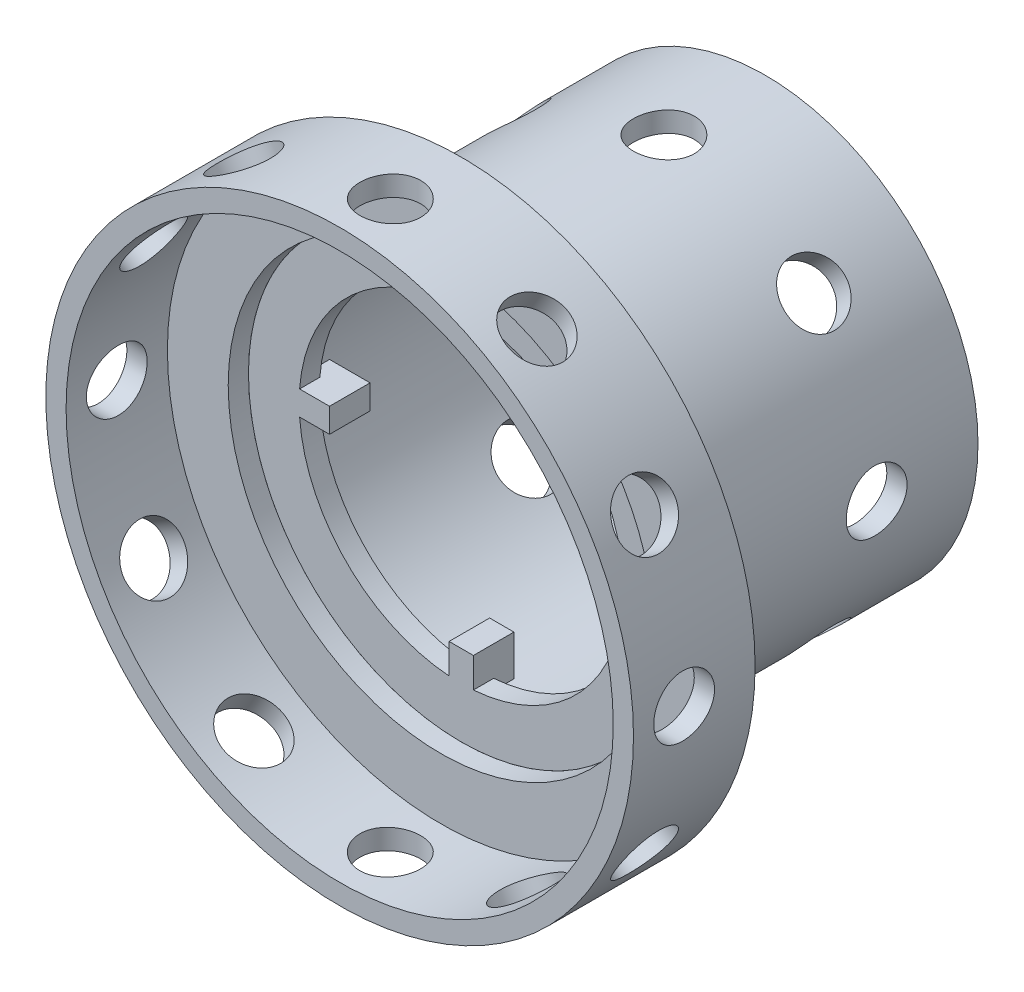
SolidWorks part; units mm, degrees
ref_plane "正面" through (0, 0, 0) normal (0, 0, 1) x (1, 0, 0)
ref_plane "平面" through (0, 0, 0) normal (0, 1, 0) x (1, 0, 0)
ref_plane "右側面" through (0, 0, 0) normal (1, 0, 0) x (0, 0, -1)
sketch "ｽｹｯﾁ1" plane through (0, 0, 0) normal (0, 0, 1) x (1, 0, 0)
  circle A0 centre (0, 0) radius 10.5
  circle A1 centre (0, 0) radius 9.5
  dimension "D1" = 21
  dimension "D2" = 19
extrude "ﾎﾞｽ - 押し出し1" add sketch "ｽｹｯﾁ1" along normal blind 15 from offset 10
sketch "ｽｹｯﾁ2" plane through (0, 0, 0) normal (0, 0, 1) x (1, 0, 0)
  circle A0 centre (0, 0) radius 10.5
  dimension "D1" = 21
extrude "ﾎﾞｽ - 押し出し2" [suppressed] add sketch "ｽｹｯﾁ2" along normal blind 1
sketch "ｽｹｯﾁ3" plane through (0, 0, 0) normal (0, 0, 1) x (1, 0, 0)
  circle A0 centre (4.4131, 3.5977) radius 0.493
extrude "ｶｯﾄ - 押し出し1" [suppressed] cut sketch "ｽｹｯﾁ3" along normal blind 1
sketch "ｽｹｯﾁ4" plane through (0, 0, 0) normal (0, 0, 1) x (1, 0, 0)
  circle A0 centre (0, 0) radius 7.5
  dimension "D1" = 15
sketch "ｽｹｯﾁ5" plane through (0, 0, 25) normal (0, 0, 1) x (1, 0, 0)
  line L1 (8.5, -0.6) -> (6.5, -0.6)
  line L2 (8.5, -0.6) -> (8.5, 0.6)
  line L3 (8.5, 0.6) -> (6.5, 0.6)
  line L4 (6.5, -0.6) -> (6.5, 0.6)
  line L5 (8.5, -0.6) -> (6.5, 0.6) construction
  line L6 (8.5, 0.6) -> (6.5, -0.6) construction
  circle A0 centre (0, 0) radius 7.5 construction
  point P0 (7.5, 0)
  point P8 (10.5, 0)
  dimension "D1" = 1.2
  dimension "D2" = 2
sketch "ｽｹｯﾁ6" plane through (0, 0, 0) normal (0, 0, 1) x (1, 0, 0)
  circle A0 centre (0, 0) radius 10
  circle A1 centre (0, 0) radius 8
  dimension "D1" = 20
  dimension "D2" = 16
extrude "ﾎﾞｽ - 押し出し3" add sketch "ｽｹｯﾁ6" against normal blind 1 from offset 25
extrude "ﾎﾞｽ - 押し出し4" add sketch "ｽｹｯﾁ5" against normal blind 2
pattern_circular "円形ﾊﾟﾀｰﾝ1" count 4 over 360 about axis through (0, 0, 0) along (0, 0, 1) of "ﾎﾞｽ - 押し出し4"
sketch "ｽｹｯﾁ7" plane through (0, 0, 0) normal (1, 0, 0) x (0, 0, -1)
  line L0 (-10, -10.5) -> (-10, 10.5) construction
  circle A0 centre (-15, 0) radius 1.5
  dimension "D1" = 3
  dimension "D2" = 5
extrude "ｶｯﾄ - 押し出し2" cut sketch "ｽｹｯﾁ7" against normal blind 20 and the other way blind 20
pattern_circular "円形ﾊﾟﾀｰﾝ2" count 8 over 360 about axis through (0, 0, 24) along (0, 0, 1) of "ｶｯﾄ - 押し出し2"
sketch "ｽｹｯﾁ8" plane through (0, 0, 25) normal (0, 0, 1) x (1, 0, 0)
  circle A0 centre (0, 0) radius 14.5
  circle A1 centre (0, 0) radius 10.5
  dimension "D1" = 29
extrude "ﾎﾞｽ - 押し出し5" add sketch "ｽｹｯﾁ8" along normal blind 6 separate body
sketch "ｽｹｯﾁ9" plane through (0, 0, 31) normal (0, 0, -1) x (-1, 0, 0)
  circle A0 centre (0, 0) radius 13.5
  dimension "D1" = 27
extrude "ｶｯﾄ - 押し出し3" cut sketch "ｽｹｯﾁ9" along normal blind 5
sketch "ｽｹｯﾁ10" plane through (0, 0, 0) normal (1, 0, 0) x (0, 0, -1)
  line L0 (-31, 14.5) -> (-31, -14.5) construction
  circle A0 centre (-28.5, 0) radius 1.5
  dimension "D1" = 3
  dimension "D2" = 2.5
extrude "ｶｯﾄ - 押し出し4" cut sketch "ｽｹｯﾁ10" along normal through all
pattern_circular "円形ﾊﾟﾀｰﾝ4" count 12 over 360 about axis through (0, 0, 31) along (0, 0, -1) of "ｶｯﾄ - 押し出し4"
